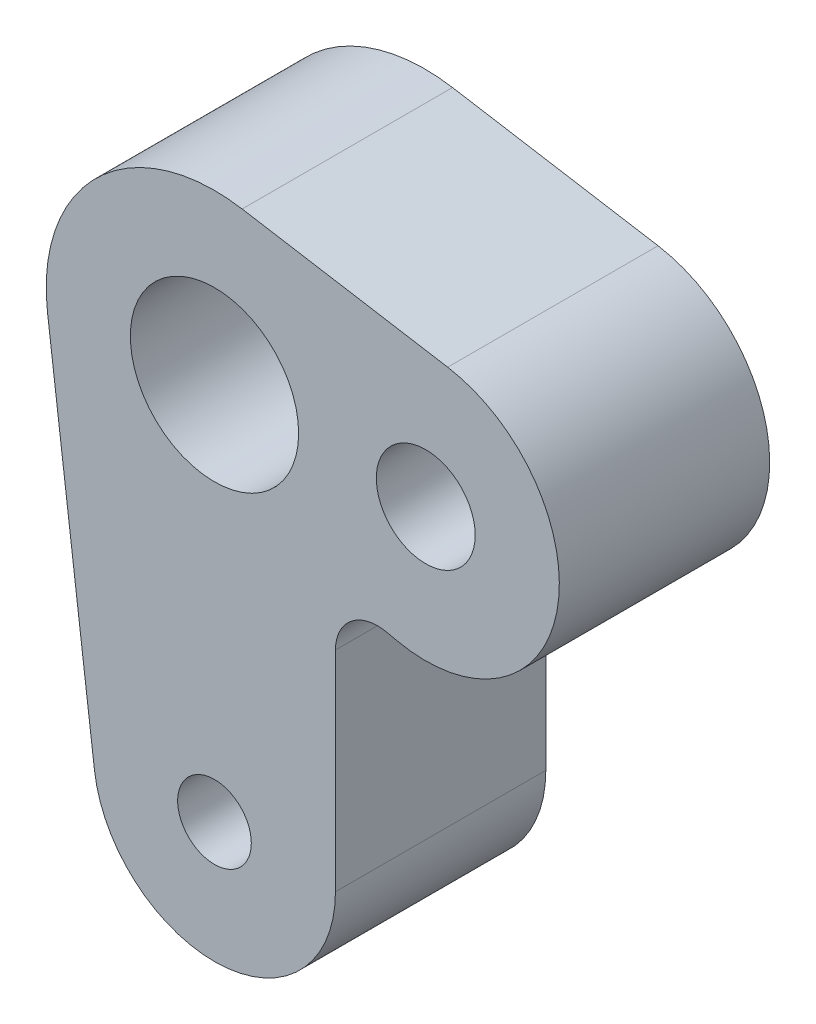
SolidWorks part; units mm, degrees
ref_plane "Front Plane" through (0, 0, 0) normal (0, 0, 1) x (1, 0, 0)
ref_plane "Top Plane" through (0, 0, 0) normal (0, 1, 0) x (1, 0, 0)
ref_plane "Right Plane" through (0, 0, 0) normal (1, 0, 0) x (0, 0, -1)
sketch "Sketch1" plane through (0, 0, 0) normal (0, 0, 1) x (1, 0, 0)
  line L0 (0, 0) -> (0, -18) construction
  line L1 (0, -18) -> (10.0423, 0) construction
  line L2 (10.0423, 0) -> (0, 0) construction
  line L3 (-7.9373, -1) -> (-5.7049, -18.7188)
  line L4 (5.75, -18) -> (5.75, -8.0462)
  line L5 (8.1768, -6.0922) -> (8.6873, -6.2037)
  line L6 (11.0857, 6.2637) -> (1.3144, 7.8913)
  circle A0 centre (10.0423, 0) radius 1.5 construction
  circle A1 centre (10.0423, 0) radius 2.35
  circle A2 centre (0, 0) radius 4
  circle A3 centre (0, -18) radius 5.25 construction
  circle A4 centre (0, -18) radius 1.75
  circle A5 centre (0, 0) radius 8
  circle A6 centre (10.0423, 0) radius 6.35
  circle A7 centre (0, -18) radius 5.75
  arc A8 (5.75, -8.0462) -> (8.1768, -6.0922) centre (7.75, -8.0462) cw
  point P0 (0, 0)
  point P1 (10.0423, 0)
  point P2 (0, -18)
  point P29 (5.75, -5.5621)
  dimension "D4" = 3
  dimension "D5" = 4.7
  dimension "D6" = 8
  dimension "D7" = 10.5
  dimension "D8" = 3.5
  dimension "D12" = 2
  dimension "D1" = 20.6119
  dimension "D2" = 18
  dimension "D3" = 10.0423
  dimension "D9" = 4
  dimension "D10" = 4
  dimension "D11" = 4
extrude "Boss-Extrude1" add sketch "Sketch1" along normal blind 10 contours A7 A4 | A6 A5 A2 | A6 A5 A1 | A6 L6 A5 | L4 A8 L5 A6 A5 L3 A7 | A5 A6 A2 A1
